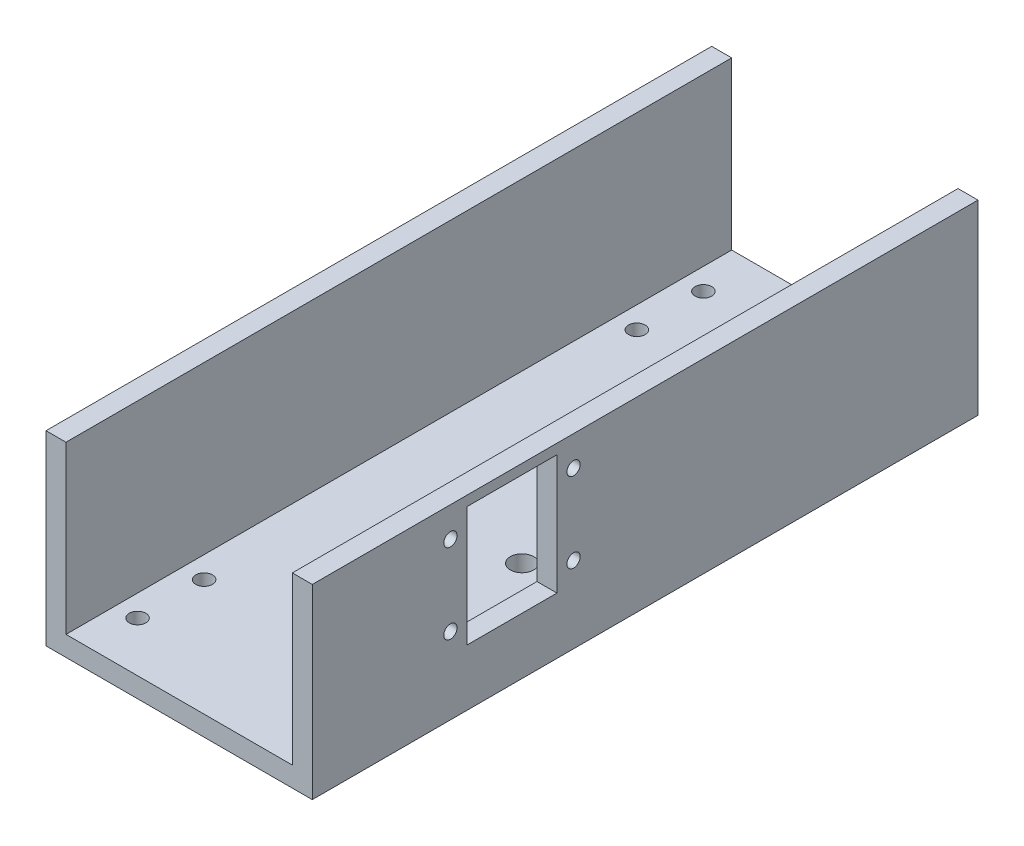
SolidWorks part; units mm, degrees
material "6061 合金"
ref_plane "前视基准面" through (0, 0, 0) normal (0, 0, 1) x (1, 0, 0)
ref_plane "上视基准面" through (0, 0, 0) normal (0, 1, 0) x (1, 0, 0)
ref_plane "右视基准面" through (0, 0, 0) normal (1, 0, 0) x (0, 0, -1)
sketch "草图1" plane through (0, 0, 0) normal (0, 0, 1) x (1, 0, 0)
  line L0 (0, 0) -> (0, 56.8781) construction
  line L1 (-40, 0) -> (40, 0)
  line L2 (40, 0) -> (40, 56)
  line L3 (40, 56) -> (34, 56)
  line L4 (34, 56) -> (34, 6)
  line L5 (34, 6) -> (-34, 6)
  line L6 (-40, 0) -> (-40, 56)
  line L7 (-40, 56) -> (-34, 56)
  line L8 (-34, 56) -> (-34, 6)
  point P8 (0, 6)
  dimension "D1" = 80
  dimension "D2" = 6
  dimension "D3" = 6
  dimension "D4" = 50
  dimension "D5" = 6
extrude "凸台-拉伸1" add sketch "草图1" along normal blind 200
sketch "草图4" plane through (0, 0, 0) normal (0, -1, 0) x (1, 0, 0)
  line L0 (27.5, 165) -> (27.5, 185) construction
  line L1 (27.5, 165) -> (-27.5, 165) construction
  line L2 (27.5, 185) -> (-27.5, 185) construction
  line L3 (-27.5, 165) -> (-27.5, 185) construction
  line L4 (27.5, 165) -> (-27.5, 185) construction
  line L5 (27.5, 185) -> (-27.5, 165) construction
  line L6 (0, 200) -> (0, 139.8429) construction
  line L7 (-40, 200) -> (40, 200) construction
  line L8 (-40, 100) -> (40, 100) construction
  line L9 (-40, 200) -> (-40, 0) construction
  line L10 (40, 200) -> (40, 0) construction
  line L11 (0, 0) -> (0, 60.1571) construction
  line L12 (27.5, 15) -> (-27.5, 35) construction
  line L13 (27.5, 35) -> (-27.5, 15) construction
  line L14 (-27.5, 35) -> (-27.5, 15) construction
  line L15 (27.5, 15) -> (-27.5, 15) construction
  line L16 (27.5, 35) -> (-27.5, 35) construction
  line L17 (27.5, 35) -> (27.5, 15) construction
  circle A0 centre (-27.5, 185) radius 2.5
  circle A1 centre (27.5, 185) radius 2.5
  circle A2 centre (-27.5, 165) radius 2.5
  circle A4 centre (27.5, 35) radius 2.5
  circle A5 centre (-27.5, 35) radius 2.5
  circle A6 centre (27.5, 15) radius 2.5
  circle A7 centre (-27.5, 15) radius 2.5
  point P1 (0, 175)
  point P29 (0, 25)
  dimension "D4" = 5
  dimension "D5" = 5
  dimension "D6" = 5
  dimension "D1" = 55
  dimension "D2" = 15
  dimension "D3" = 20
extrude "切除-拉伸2" cut sketch "草图4" against normal up to next
sketch "草图3" plane through (40, 0, 0) normal (1, 0, 0) x (0, 0, -1)
  line L0 (-200, 30) -> (-140, 30) construction
  line L2 (-158, 37.2595) -> (-158, 30) construction
  line L3 (-140, 30) -> (-140, 59.236) construction
  line L4 (-200, 0) -> (0, 0) construction
  line L5 (-200, 0) -> (-200, 56) construction
  circle A0 centre (-140, 30) radius 5
  circle A1 centre (-158, 30) radius 2.5
  circle A2 centre (-122, 30) radius 2.5
  dimension "D1" = 60
  dimension "D2" = 5
  dimension "D4" = 10
  dimension "D5" = 30
  dimension "D3" = 18
sketch "草图6" plane through (0, 6, 0) normal (0, 1, 0) x (1, 0, 0)
  circle A0 centre (13, -123.5) radius 2.5
  circle A1 centre (13, -155.5) radius 2.5
  dimension "D1" = 5
  dimension "D2" = 5
sketch "草图8" plane through (40, 0, 0) normal (1, 0, 0) x (0, 0, -1)
  line L0 (-140, 30) -> (-140, 59.236) construction
  line L1 (-126.5, 17) -> (-153.5, 17)
  line L2 (-126.5, 17) -> (-126.5, 53)
  line L3 (-126.5, 53) -> (-153.5, 53)
  line L4 (-153.5, 17) -> (-153.5, 53)
  line L5 (-140, 30) -> (-140, 50.4271) construction
  line L6 (-200, 56) -> (0, 56) construction
  circle A0 centre (-121.5, 23) radius 2
  circle A1 centre (-121.5, 47) radius 2
  circle A2 centre (-158.5, 47) radius 2
  circle A3 centre (-158.5, 23) radius 2
  dimension "D1" = 3
  dimension "D2" = 4
  dimension "D3" = 27
  dimension "D4" = 4
  dimension "D5" = 36
  dimension "D6" = 6
  dimension "D7" = 6
  dimension "D8" = 5
  dimension "D9" = 5
extrude "切除-拉伸5" cut sketch "草图8" against normal blind 10
sketch "草图9" plane through (0, 6, 0) normal (0, 1, 0) x (1, 0, 0)
  line L0 (-40, -200) -> (40, -200) construction
  line L1 (40, -200) -> (40, -140) construction
  circle A0 centre (16, -166) radius 3.5
  dimension "D3" = 7
  dimension "D1" = 34
  dimension "D2" = 24
extrude "切除-拉伸6" cut sketch "草图9" against normal blind 10
sketch "草图10" plane through (0, 6, 0) normal (0, 1, 0) x (1, 0, 0)
  line L0 (16, -166) -> (16, -113) construction
  line L2 (16, -139.5) -> (26.105, -139.5) construction
  circle A0 centre (16, -113) radius 3.5
  circle A1 centre (16, -166) radius 3.5 construction
  circle A2 centre (16, -166) radius 3.5
  dimension "D2" = 7
  dimension "D1" = 53
extrude "切除-拉伸7" cut sketch "草图10" against normal blind 10
